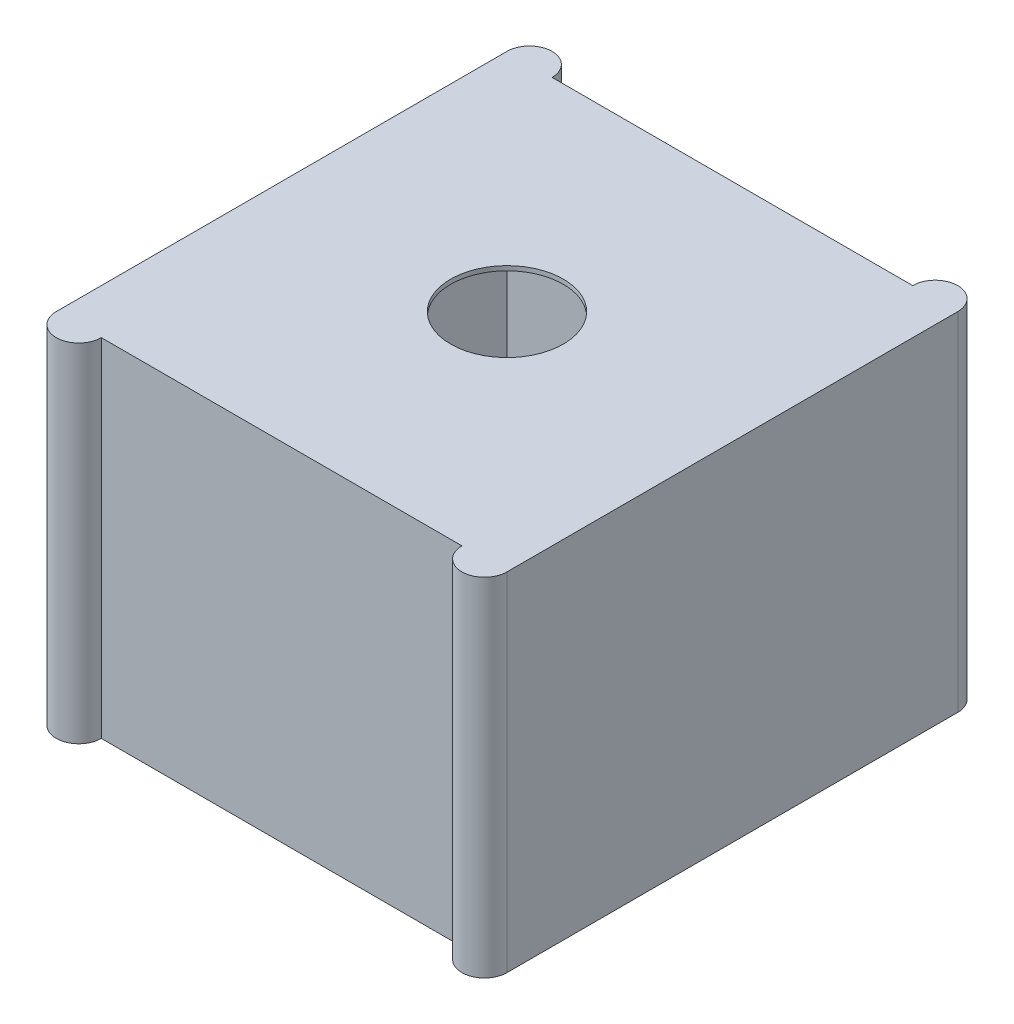
SolidWorks part; units mm, degrees
ref_plane "Front Plane" through (0, 0, 0) normal (0, 0, 1) x (1, 0, 0)
ref_plane "Top Plane" through (0, 0, 0) normal (0, 1, 0) x (1, 0, 0)
ref_plane "Right Plane" through (0, 0, 0) normal (1, 0, 0) x (0, 0, -1)
sketch "Sketch1" plane through (0, 0, 0) normal (0, 1, 0) x (1, 0, 0)
  line L0 (0, 0) -> (0, -164.7719) construction
  line L1 (-80, 100) -> (80, 100)
  line L2 (-100, 100) -> (-100, -100)
  line L3 (-80, -100) -> (80, -100)
  line L4 (100, 100) -> (100, -100)
  line L5 (-100, 100) -> (100, -100) construction
  line L6 (-100, -100) -> (100, 100) construction
  line L7 (0, 0) -> (230.7692, 0) construction
  arc A0 (-100, 100) -> (-80, 100) centre (-90, 100) cw
  arc A1 (100, 100) -> (80, 100) centre (90, 100) ccw
  arc A2 (100, -100) -> (80, -100) centre (90, -100) cw
  arc A3 (-100, -100) -> (-80, -100) centre (-90, -100) ccw
  circle A4 centre (0, 0) radius 25
  point P0 (0, 0)
  point P17 (-90, 110)
  point P19 (0, 0)
  point P20 (0, 0)
  dimension "D4" = 50
  dimension "D1" = 200
  dimension "D2" = 200
  dimension "D3" = 10
extrude "Boss-Extrude1" add sketch "Sketch1" along normal blind 154
ref_plane "Plane1" through (0, 152, 0) normal (0, 1, 0) x (1, 0, 0)
sketch "Sketch2" plane through (0, 152, 0) normal (0, 1, 0) x (1, 0, 0)
  line L1 (-93, 93) -> (93, 93)
  line L2 (-93, 93) -> (-93, -93)
  line L3 (-93, -93) -> (93, -93)
  line L4 (93, 93) -> (93, -93)
  line L5 (-93, 93) -> (93, -93) construction
  line L6 (-93, -93) -> (93, 93) construction
  point P0 (0, 0)
  dimension "D1" = 186
  dimension "D2" = 186
extrude "Cut-Extrude1" cut sketch "Sketch2" against normal blind 150
